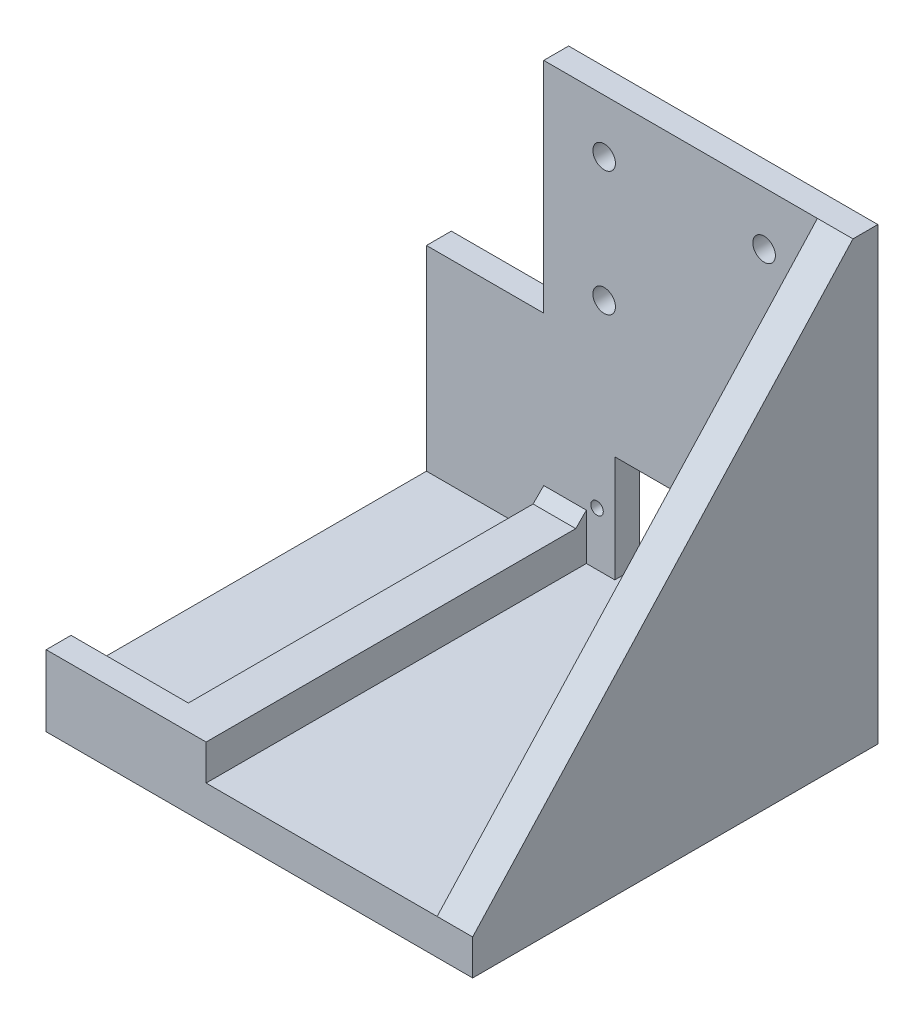
SolidWorks part; units mm, degrees
ref_plane "Front" through (0, 0, 0) normal (0, 0, 1) x (1, 0, 0)
ref_plane "Top" through (0, 0, 0) normal (0, 1, 0) x (1, 0, 0)
ref_plane "Right" through (0, 0, 0) normal (1, 0, 0) x (0, 0, -1)
sketch "Sketch1" plane through (0, 0, 0) normal (0, 1, 0) x (1, 0, 0)
  line L1 (-55, -57) -> (55, -57)
  line L2 (-55, -57) -> (-55, 57)
  line L3 (-55, 57) -> (55, 57)
  line L4 (55, -57) -> (55, 57)
  line L5 (-55, -57) -> (55, 57) construction
  line L6 (-55, 57) -> (55, -57) construction
  point P0 (0, 0)
  dimension "D1" = 110
  dimension "D2" = 114
extrude "Boss-Extrude1" add sketch "Sketch1" against normal blind 10
sketch "Sketch3" plane through (0, 0, 0) normal (0, 1, 0) x (1, 0, 0)
  line L0 (-55, -50) -> (-55, -57)
  line L2 (-55, -57) -> (-10, -57)
  line L4 (-10, -57) -> (-10, 57)
  line L5 (-10, 57) -> (-55, 57)
  line L7 (-55, 57) -> (-55, 50)
  line L8 (-55, 50) -> (-22, 50)
  line L9 (-22, 50) -> (-22, -50)
  line L10 (-22, -50) -> (-55, -50)
  line L11 (-55, 57) -> (-55, -57) construction
  point P2 (-40, 23.8043)
  point P8 (-40, 32)
  point P11 (40, 32)
  point P12 (0, 0)
  point P17 (40, -32)
  point P21 (-40, -32)
  dimension "D1" = 7
  dimension "D2" = 12
  dimension "D3" = 33
extrude "Boss-Extrude2" add sketch "Sketch3" along normal blind 10
sketch "Sketch4" plane through (0, 0, 0) normal (0, 1, 0) x (1, 0, 0)
  line L0 (55, 57) -> (-55, 57)
  line L2 (-10, 57) -> (-55, 57) construction
  line L3 (-55, 50) -> (-55, 57) construction
  line L4 (-55, 57) -> (-55, 50)
  line L5 (-55, 50) -> (55, 50)
  line L6 (55, 50) -> (55, 57)
  line L7 (-22, 50) -> (-55, 50) construction
  point P2 (0, 0)
  point P3 (60, 32)
  point P8 (20, 27.2254)
  point P15 (0, 0)
extrude "Boss-Extrude3" add sketch "Sketch4" along normal up to surface (116.6 mm away)
sketch "Sketch12" plane through (0, 116.6, 0) normal (0, 1, 0) x (1, 0, 0)
  line L0 (-55, 50) -> (55, 50) construction
  line L1 (-55, 50) -> (-22, 50)
  line L2 (-55, 50) -> (-55, 57)
  line L3 (-55, 57) -> (-22, 57)
  line L4 (-22, 50) -> (-22, 57)
  line L5 (55, 57) -> (-55, 57) construction
  line L6 (-22, 50) -> (-22, -50) construction
  point P8 (0, 0)
  point P9 (0, 0)
  point P10 (0, 0)
  point P13 (-51.9015, 57)
  point P14 (-50.1167, 50)
  point P15 (0, 0)
extrude "Cut-Extrude6" cut sketch "Sketch12" against normal up to surface (61.6 mm away)
sketch "Sketch8" plane through (0, 0, -50) normal (0, 0, 1) x (1, 0, 0)
  line L1 (-2, 0) -> (24, 0)
  line L2 (-2, 0) -> (-2, 30)
  line L3 (-2, 30) -> (24, 30)
  line L4 (24, 0) -> (24, 30)
  line L5 (-10, 10) -> (-10, 0) construction
  line L6 (-10, 0) -> (55, 0) construction
  point P4 (-2, 0)
  dimension "D1" = 8
  dimension "D2" = 26
  dimension "D3" = 30
extrude "Cut-Extrude3" cut sketch "Sketch8" against normal through all
sketch "Sketch9" plane through (0, 0, -50) normal (0, 0, 1) x (1, 0, 0)
  line L1 (37, 22.5) -> (50, 22.5)
  line L2 (37, 22.5) -> (37, 3)
  line L3 (37, 3) -> (50, 3)
  line L4 (50, 22.5) -> (50, 3)
  line L6 (24, 0) -> (24, 30) construction
  line L9 (24, 0) -> (55, 0) construction
  point P4 (44.3762, -2.8947)
  dimension "D1" = 3
  dimension "D2" = 19.5
  dimension "D3" = 13
  dimension "D4" = 13
extrude "Cut-Extrude4" cut sketch "Sketch9" against normal through all
sketch "Sketch10" plane through (0, 0, -50) normal (0, 0, 1) x (1, 0, 0)
  line L23 (35, 1) -> (52, 1)
  line L24 (52, 1) -> (52, 24.5)
  line L25 (35, 24.5) -> (35, 1)
  line L26 (52, 24.5) -> (35, 24.5)
  line L27 (35, 1) -> (52, 1)
  line L28 (52, 1) -> (52, 24.5)
  line L29 (35, 24.5) -> (35, 1)
  line L30 (52, 24.5) -> (35, 24.5)
  dimension "D1" = 2
extrude "Cut-Extrude5" cut sketch "Sketch10" against normal blind 4
sketch "Sketch6" plane through (0, 0, -50) normal (0, 0, 1) x (1, 0, 0)
  line L1 (-22, 116.6) -> (55, 116.6) construction
  line L3 (55, 116.6) -> (55, 0) construction
  line L4 (-5, 101.6) -> (40, 101.6) construction
  line L5 (-5, 66.6) -> (40, 66.6) construction
  circle A0 centre (-5, 101.6) radius 3.175
  circle A1 centre (40, 101.6) radius 3.175
  circle A3 centre (-5, 66.6) radius 3.175
  circle A4 centre (40, 66.6) radius 3.175
  dimension "D2" = 6.35
  dimension "D5" = 2
  dimension "D1" = 15
  dimension "D3" = 15
  dimension "D4" = 45
extrude "Cut-Extrude1" cut sketch "Sketch6" against normal through all
sketch "Sketch11" plane through (55, 0, 0) normal (1, 0, 0) x (0, 0, -1)
  line L0 (57, 116.6) -> (50, 116.6)
  line L1 (50, 116.6) -> (50, 0) construction
  line L2 (57, 116.6) -> (50, 116.6) construction
  line L3 (50, 116.6) -> (-57, 0)
  line L4 (-57, -10) -> (-57, 0) construction
  line L5 (-57, 0) -> (-57, -10)
  line L6 (-57, -10) -> (57, -10)
  line L7 (-57, -10) -> (57, -10) construction
  line L8 (57, -10) -> (57, 116.6)
  line L9 (-57, 0) -> (50, 0) construction
  line L10 (57, -10) -> (57, 116.6) construction
  point P13 (-57, 0)
  point P16 (57, -5)
extrude "Boss-Extrude5" add sketch "Sketch11" along normal blind 10
sketch "Sketch14" plane through (0, 0, -57) normal (0, 0, -1) x (-1, 0, 0)
  line L0 (-24, 0) -> (-55, 0) construction
  line L1 (-24, 0) -> (-24, 30) construction
  circle A0 centre (-29, 15) radius 1.75
  circle A1 centre (7, 15) radius 1.75
  point P6 (0, 0)
  dimension "D1" = 3.5
  dimension "D2" = 36
  dimension "D3" = 15
  dimension "D4" = 5
extrude "Cut-Extrude7" cut sketch "Sketch14" against normal through all
chamfer "Chamfer2" distance 3 angle 45 1 edges at (-16, 10, -50)
